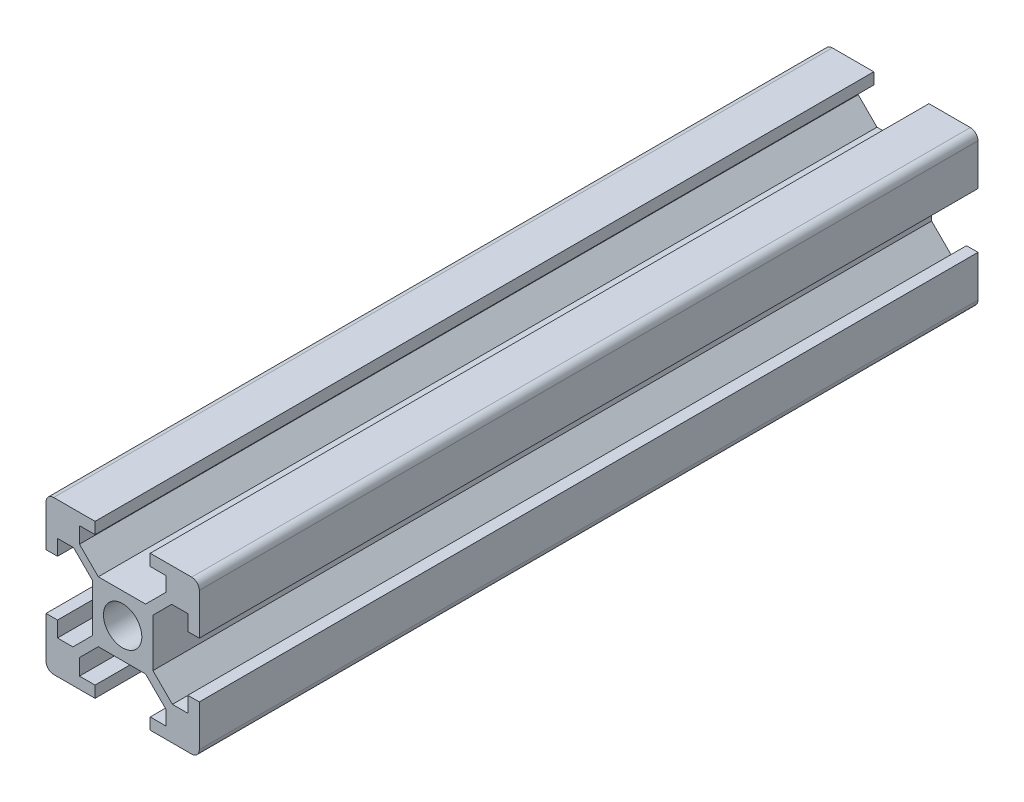
SolidWorks part; units mm, degrees
ref_plane "Front Plane" through (0, 0, 0) normal (0, 0, 1) x (1, 0, 0)
ref_plane "Top Plane" through (0, 0, 0) normal (0, 1, 0) x (1, 0, 0)
ref_plane "Right Plane" through (0, 0, 0) normal (1, 0, 0) x (0, 0, -1)
sketch "Sketch1" plane through (0, 0, 0) normal (0, 0, 1) x (1, 0, 0)
  line L0 (-9, -10) -> (-3.6, -10) construction
  line L1 (-9, 10) -> (-3.6, 10)
  line L2 (-10, 9) -> (-10, 3.6)
  line L3 (3.6, -10) -> (9, -10)
  line L4 (10, 9) -> (10, 3.6)
  line L7 (-3.178, 3.95) -> (2.9913, 3.95)
  line L8 (-3.95, 3.178) -> (-3.95, -3.0886)
  line L9 (-3.178, -3.95) -> (2.9913, -3.95)
  line L10 (3.95, 3.178) -> (3.95, -3.0886)
  line L13 (9, -10) -> (3.6, -10) construction
  line L14 (10, 9) -> (10, 3.6)
  line L15 (10, -9) -> (10, -3.6)
  line L16 (-10, -9) -> (-10, -3.6)
  line L17 (-10, 9) -> (-10, 3.6)
  line L18 (-9, 10) -> (-3.6, 10)
  line L19 (9, 10) -> (3.6, 10)
  line L20 (3.6, 10) -> (9, 10)
  line L21 (-10, -3.6) -> (-10, -9)
  line L22 (10, -3.6) -> (10, -9)
  line L23 (-3.6, -10) -> (-9, -10)
  line L24 (-5.63, 6.402) -> (-3.178, 3.95)
  line L25 (-9, 10) -> (-5.63, 10)
  line L26 (-10, 9) -> (-10, 5.63)
  line L27 (-8.5, 5.63) -> (-6.402, 5.63)
  line L28 (-5.63, 8.5) -> (-5.63, 6.402)
  line L29 (9, 10) -> (5.63, 10)
  line L30 (10, 9) -> (10, 5.63)
  line L31 (8.5, 5.63) -> (6.402, 5.63)
  line L32 (5.63, 8.5) -> (5.63, 6.5887)
  line L33 (-9, -10) -> (-5.63, -10)
  line L34 (-10, -9) -> (-10, -5.63)
  line L35 (-8.5, -5.63) -> (-6.4914, -5.63)
  line L36 (-5.63, -8.5) -> (-5.63, -6.402)
  line L37 (9, -10) -> (5.63, -10)
  line L38 (10, -9) -> (10, -5.63)
  line L39 (8.5, -5.63) -> (6.4914, -5.63)
  line L40 (5.63, -8.5) -> (5.63, -6.5887)
  line L41 (-5.63, 10) -> (-3.6, 10)
  line L43 (-5.63, 8.5) -> (-3.6, 8.5)
  line L44 (-3.6, 10) -> (-3.6, 8.5)
  line L45 (-10, 3.6) -> (-8.5, 3.6)
  line L46 (-10, 3.6) -> (-10, 5.63)
  line L48 (-8.5, 3.6) -> (-8.5, 5.63)
  line L49 (-10, -3.6) -> (-8.5, -3.6)
  line L50 (-10, -3.6) -> (-10, -5.63)
  line L52 (-8.5, -3.6) -> (-8.5, -5.63)
  line L53 (-5.63, -10) -> (-3.6, -10)
  line L55 (-5.63, -8.5) -> (-3.6, -8.5)
  line L56 (-3.6, -10) -> (-3.6, -8.5)
  line L57 (3.6, -10) -> (5.63, -10)
  line L58 (3.6, -10) -> (3.6, -8.5)
  line L59 (3.6, -8.5) -> (5.63, -8.5)
  line L61 (10, -3.6) -> (8.5, -3.6)
  line L62 (10, -3.6) -> (10, -5.63)
  line L64 (8.5, -3.6) -> (8.5, -5.63)
  line L65 (10, 3.6) -> (8.5, 3.6)
  line L66 (10, 3.6) -> (10, 5.63)
  line L68 (8.5, 3.6) -> (8.5, 5.63)
  line L69 (3.6, 10) -> (5.63, 10)
  line L70 (3.6, 10) -> (3.6, 8.5)
  line L71 (3.6, 8.5) -> (5.63, 8.5)
  line L73 (-6.402, 5.63) -> (-3.95, 3.178)
  line L74 (2.9913, 3.95) -> (5.63, 6.5887)
  line L75 (3.95, 3.178) -> (6.402, 5.63)
  line L76 (3.95, -3.0886) -> (6.4914, -5.63)
  line L77 (2.9913, -3.95) -> (5.63, -6.5887)
  line L78 (-3.95, -3.0886) -> (-6.4914, -5.63)
  line L79 (-3.178, -3.95) -> (-5.63, -6.402)
  circle A0 centre (0, 0) radius 2.5
  arc A1 (10, 9) -> (9, 10) centre (9, 9) ccw
  arc A2 (10, -9) -> (9, -10) centre (9, -9) cw
  arc A3 (-9, -10) -> (-10, -9) centre (-9, -9) cw
  arc A4 (-10, 9) -> (-9, 10) centre (-9, 9) cw
  point P0 (0, 0)
  dimension "D3" = 5
  dimension "D4" = 1
  dimension "D5" = 1
  dimension "D15" = 1.5
  dimension "D16" = 1.5
  dimension "D17" = 1.5
  dimension "D18" = 1.5
  dimension "D19" = 1.5
  dimension "D20" = 1.5
  dimension "D21" = 1.5
  dimension "D22" = 1.5
extrude "Boss-Extrude1" add sketch "Sketch1" along normal blind 482.6 contours A4 L2 L17 L45 L48 L27 L73 L8 L78 L35 L52 L49 L21 L16 A3 L23 L56 L55 L36 L79 L9 L77 L40 L59 L58 L3 A2 L15 L22 L61 L64 L39 L76 L10 L75 L31 L68 L65 L14 L4 A1 L19 L20 L70 L71 L32 L74 L7 L24
sketch "Sketch2" plane through (0, 10, 0) normal (0, 1, 0) x (1, 0, 0)
  line L1 (-14.1357, 0) -> (21.8538, 0) construction
  line L2 (-14.1357, 0) -> (-14.1357, -101.6) construction
  line L3 (-14.1357, -101.6) -> (21.8538, -101.6) construction
  line L4 (21.8538, 0) -> (21.8538, -101.6) construction
  line L5 (-14.1357, -101.6) -> (21.8538, -101.6)
  line L6 (-14.1357, -101.6) -> (-14.1357, -499.1237)
  line L7 (-14.1357, -499.1237) -> (21.8538, -499.1237)
  line L8 (21.8538, -101.6) -> (21.8538, -499.1237)
  dimension "D1" = 101.6
extrude "Cut-Extrude1" cut sketch "Sketch2" against normal through all
